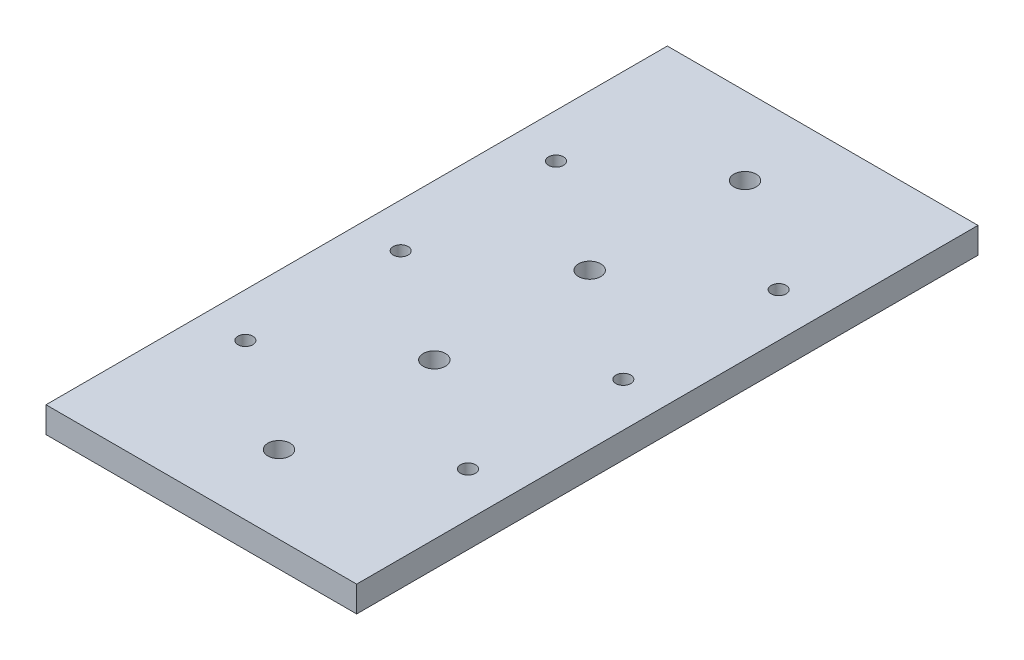
SolidWorks part; units mm, degrees
ref_plane "Front Plane" through (0, 0, 0) normal (0, 0, 1) x (1, 0, 0)
ref_plane "Top Plane" through (0, 0, 0) normal (0, 1, 0) x (1, 0, 0)
ref_plane "Right Plane" through (0, 0, 0) normal (1, 0, 0) x (0, 0, -1)
sketch "Sketch1" plane through (0, 0, 0) normal (0, 1, 0) x (1, 0, 0)
  line L0 (0, 76.2) -> (0, 57.15) construction
  line L1 (-38.1, 76.2) -> (38.1, 76.2)
  line L2 (-38.1, 76.2) -> (-38.1, -76.2)
  line L3 (-38.1, -76.2) -> (38.1, -76.2)
  line L4 (38.1, 76.2) -> (38.1, -76.2)
  line L5 (-38.1, 76.2) -> (38.1, -76.2) construction
  line L6 (-38.1, -76.2) -> (38.1, 76.2) construction
  line L7 (0, 57.15) -> (27.305, 57.15) construction
  line L8 (27.305, 57.15) -> (27.305, 38.1) construction
  circle A0 centre (0, 57.15) radius 2.7305
  circle A1 centre (0, 19.05) radius 2.7305
  circle A2 centre (0, -19.05) radius 2.7305
  circle A3 centre (0, -57.15) radius 2.7305
  circle A4 centre (27.305, 38.1) radius 1.8288
  circle A5 centre (27.305, 0) radius 1.8288
  circle A6 centre (27.305, -38.1) radius 1.8288
  circle A7 centre (-27.305, 0) radius 1.8288
  circle A8 centre (-27.305, -38.1) radius 1.8288
  circle A9 centre (-27.305, 38.1) radius 1.8288
  point P0 (0, 0)
  dimension "D4" = 5.461
  dimension "D10" = 3.6576
  dimension "D1" = 76.2
  dimension "D2" = 152.4
  dimension "D3" = 19.05
  dimension "D6" = 27.305
  dimension "D7" = 19.05
  dimension "D5" = 4
  dimension "D8" = 3
  dimension "D9" = 2
extrude "Boss-Extrude1" add sketch "Sketch1" against normal blind 6.35
